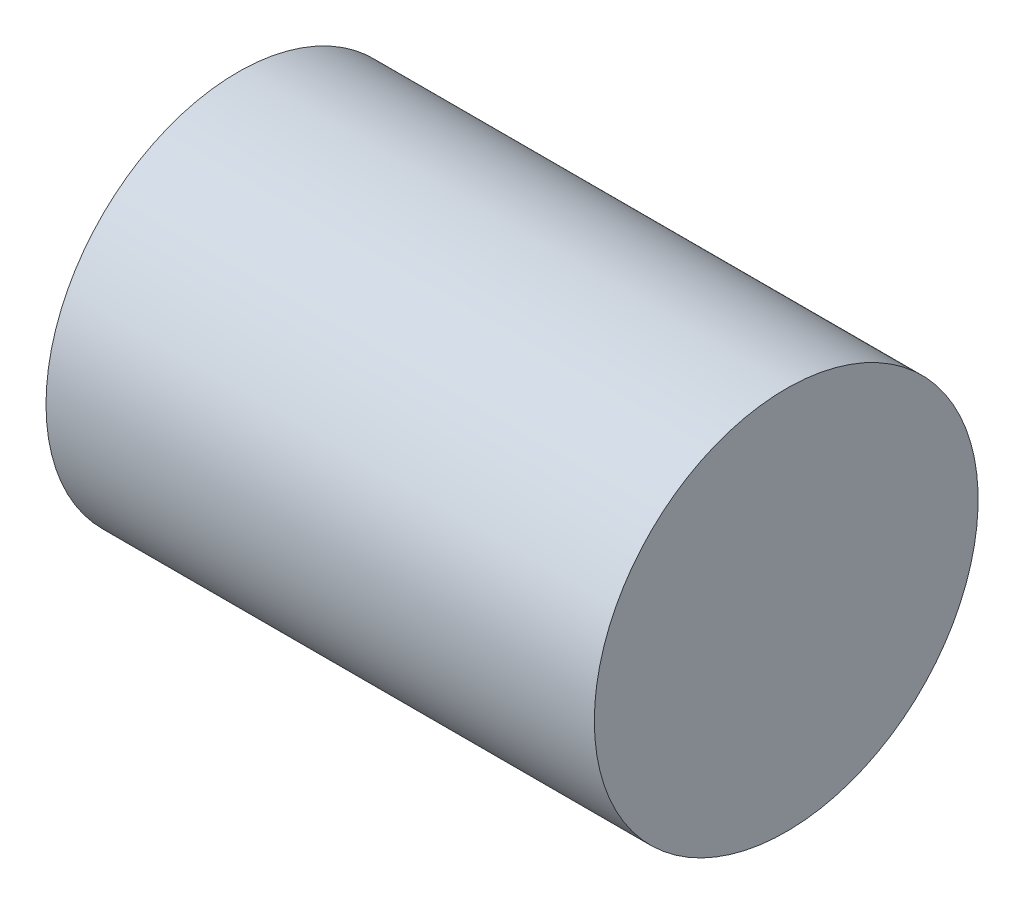
SolidWorks part; units mm, degrees
material "1023 al carbonio, lamiera (SS)"
ref_plane "Piano frontale" through (0, 0, 0) normal (0, 0, 1) x (1, 0, 0)
ref_plane "Piano superiore" through (0, 0, 0) normal (0, 1, 0) x (1, 0, 0)
ref_plane "Piano destro" through (0, 0, 0) normal (1, 0, 0) x (0, 0, -1)
sketch "Schizzo1" plane through (0, 0, 0) normal (0, 0, 1) x (1, 0, 0)
  line L1 (0, 0) -> (40, 0)
  line L2 (0, 0) -> (0, 14)
  line L3 (0, 14) -> (40, 14)
  line L4 (40, 0) -> (40, 14)
  dimension "D1" = 14
  dimension "D2" = 40
revolve "Rivoluzione1" add sketch "Schizzo1" angle 360 about L3
